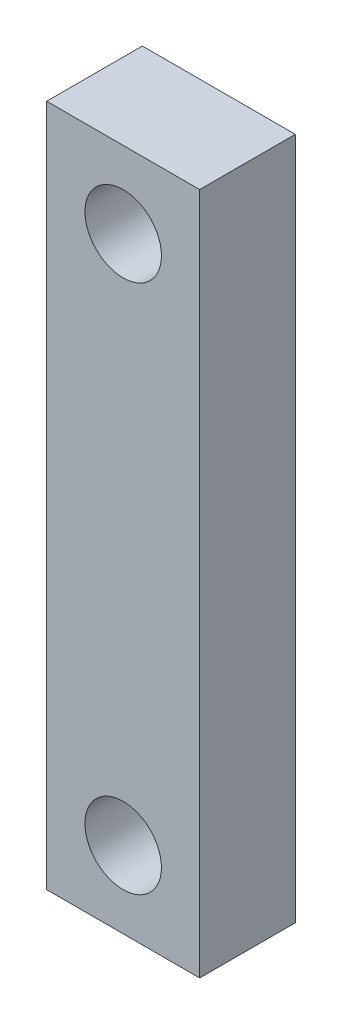
SolidWorks part; units mm, degrees
material "AISI 304"
ref_plane "Front Plane" through (0, 0, 0) normal (0, 0, 1) x (1, 0, 0)
ref_plane "Top Plane" through (0, 0, 0) normal (0, 1, 0) x (1, 0, 0)
ref_plane "Right Plane" through (0, 0, 0) normal (1, 0, 0) x (0, 0, -1)
sketch "Sketch1" plane through (0, 0, 0) normal (0, 0, 1) x (1, 0, 0)
  line L1 (-8, 35.7) -> (8, 35.7)
  line L2 (-8, 35.7) -> (-8, -35.7)
  line L3 (-8, -35.7) -> (8, -35.7)
  line L4 (8, 35.7) -> (8, -35.7)
  dimension "D1" = 8
  dimension "D2" = 8
  dimension "D3" = 35.7
  dimension "D4" = 35.7
  dimension "D5" = 71.4
  dimension "D6" = 16
extrude "Body" add sketch "Sketch1" along normal mid plane 10
sketch "Sketch2" plane through (0, 0, 5) normal (0, 0, 1) x (1, 0, 0)
  line L0 (0, -42.378) -> (0, 40.1391) construction
  circle A0 centre (0, 27.7) radius 4
  dimension "D1" = 8
  dimension "D2" = 27.7
extrude "Top Hole" cut sketch "Sketch2" against normal through all
mirror "Bottom Hole" about plane through (0, 0, 0) normal (0, 1, 0) of "Top Hole"
